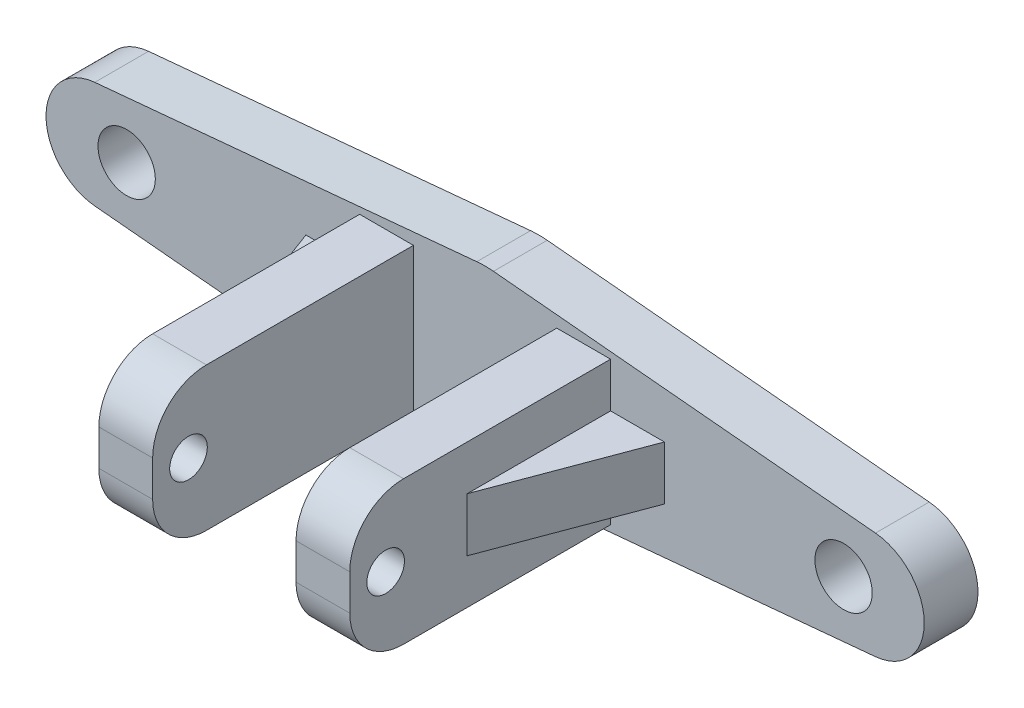
SolidWorks part; units mm, degrees
ref_plane "前视基准面" through (0, 0, 0) normal (0, 0, 1) x (1, 0, 0)
ref_plane "上视基准面" through (0, 0, 0) normal (0, 1, 0) x (1, 0, 0)
ref_plane "右视基准面" through (0, 0, 0) normal (1, 0, 0) x (0, 0, -1)
other "Configuration Table"
sketch "草图1" plane through (0, 0, 0) normal (0, 0, 1) x (1, 0, 0)
  line L0 (36.2157, 0) -> (-36.2157, 0) construction
  line L5 (-21.7791, 2.987) -> (-0.4651, 4.9783)
  line L6 (-21.7791, -2.987) -> (-0.4651, -4.9783)
  line L7 (0.4651, 4.9783) -> (21.7791, 2.987)
  line L8 (21.7791, -2.987) -> (0.4651, -4.9783)
  arc A0 (0.4651, 4.9783) -> (-0.4651, 4.9783) centre (0, 0) ccw
  arc A1 (-21.7791, 2.987) -> (-21.7791, -2.987) centre (-21.5, 0) ccw
  arc A2 (21.7791, -2.987) -> (21.7791, 2.987) centre (21.5, 0) ccw
  arc A3 (-0.4651, -4.9783) -> (0.4651, -4.9783) centre (0, 0) ccw
  point P6 (0, 0)
  dimension "D1" = 10
  dimension "D4" = 6
  dimension "D5" = 6
  dimension "D2" = 21.5
  dimension "D3" = 21.5
extrude "凸台-拉伸1" add sketch "草图1" along normal blind 3
sketch "草图2" plane through (0, 0, 3) normal (0, 0, 1) x (1, 0, 0)
  line L0 (24.5, 0) -> (-24.5, 0) construction
  arc A2 (-21.7791, 2.987) -> (-21.7791, -2.987) centre (-21.5, 0) ccw construction
  circle A3 centre (-20, 0) radius 1.6
  circle A4 centre (20, 0) radius 1.6
  point P8 (0, 0)
  dimension "D1" = 3.2
  dimension "D3" = 20
  dimension "D4" = 20
  dimension "D2" = 3.2
extrude "切除-拉伸1" cut sketch "草图2" against normal through all
sketch "草图4" plane through (0, 0, 3) normal (0, 0, 1) x (1, 0, 0)
  line L1 (7, -4) -> (-7, -4)
  line L2 (7, -4) -> (7, 4)
  line L3 (7, 4) -> (-7, 4)
  line L4 (-7, -4) -> (-7, 4)
  line L5 (7, -4) -> (-7, 4) construction
  line L6 (7, 4) -> (-7, -4) construction
  point P0 (0, 0)
  dimension "D1" = 14
  dimension "D2" = 8
extrude "凸台-拉伸2" add sketch "草图4" along normal blind 14.55
sketch "草图5" plane through (0, 4, 0) normal (0, 1, 0) x (1, 0, 0)
  line L0 (7, -17.55) -> (-7, -17.55) construction
  line L1 (-4, -17.55) -> (4, -17.55)
  line L2 (-4, -17.55) -> (-4, -3)
  line L3 (-4, -3) -> (4, -3)
  line L4 (4, -17.55) -> (4, -3)
  line L5 (7, -3) -> (-7, -3) construction
  line L6 (-7, -17.55) -> (-7, -3) construction
  line L7 (7, -17.55) -> (7, -3) construction
  dimension "D1" = 3
  dimension "D2" = 3
extrude "切除-拉伸2" cut sketch "草图5" against normal through all
sketch "草图6" plane through (7, 0, 0) normal (1, 0, 0) x (0, 0, -1)
  line L0 (-17.55, 0) -> (-3, 0) construction
  line L1 (-17.55, -4) -> (-17.55, 4) construction
  line L2 (-3, 2.987) -> (-3, -2.987) construction
  circle A0 centre (-15.55, 0) radius 1.05
  dimension "D1" = 2.1
  dimension "D2" = 2
extrude "切除-拉伸3" cut sketch "草图6" against normal through all
fillet "圆角1" radius 3 4 edges at (5.5, 4, 17.55) (5.5, -4, 17.55) (-5.5, -4, 17.55) (-5.5, 4, 17.55)
ref_plane "基准面1" through (0, 0, 0) normal (0, 1, 0) x (1, 0, 0)
sketch "草图7" plane through (0, 0, 0) normal (0, 1, 0) x (1, 0, 0)
  line L0 (10, -3) -> (7, -11)
  line L1 (21.7791, -3) -> (0.4651, -3) construction
  line L2 (7, -14.55) -> (7, -3) construction
  dimension "D1" = 3
  dimension "D2" = 8
rib "筋1" sketch "草图7" sketch "草图7" thickness 3 extrusion direction parallel to sketch draft on no parameters "D1"=3
sketch "草图8" plane through (0, 0, 0) normal (0, 1, 0) x (1, 0, 0)
  line L0 (-10, -3) -> (-7, -11)
  line L1 (-0.4651, -3) -> (-21.7791, -3) construction
  line L2 (-7, -14.55) -> (-7, -3) construction
  dimension "D1" = 3
  dimension "D2" = 8
rib "筋2" sketch "草图8" sketch "草图8" thickness 3 extrusion direction parallel to sketch draft on no parameters "D1"=3
